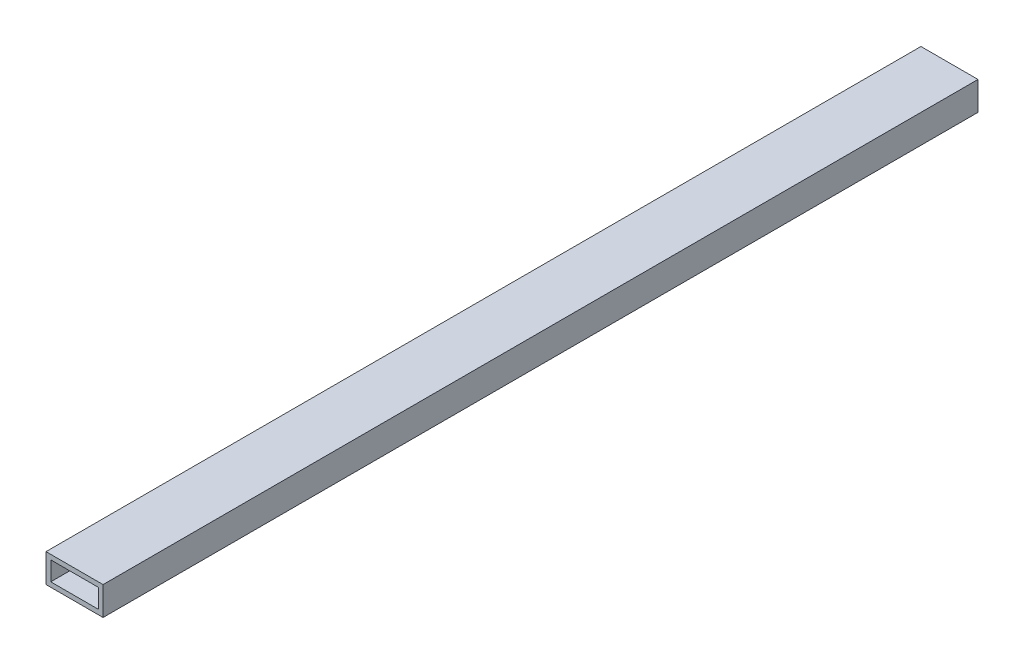
SolidWorks part; units mm, degrees
ref_plane "Front Plane" through (0, 0, 0) normal (0, 0, 1) x (1, 0, 0)
ref_plane "Top Plane" through (0, 0, 0) normal (0, 1, 0) x (1, 0, 0)
ref_plane "Right Plane" through (0, 0, 0) normal (1, 0, 0) x (0, 0, -1)
sketch "Sketch1" plane through (0, 0, 0) normal (0, 0, 1) x (1, 0, 0)
  line L1 (-12.5589, 10.0894) -> (25.5411, 10.0894)
  line L2 (-12.5589, 10.0894) -> (-12.5589, -8.9606)
  line L3 (-12.5589, -8.9606) -> (25.5411, -8.9606)
  line L4 (25.5411, 10.0894) -> (25.5411, -8.9606)
  dimension "D1" = 38.1
  dimension "D2" = 19.05
extrude "Boss-Extrude1" add sketch "Sketch1" along normal blind 584.2 contours L2 L3 L4 L1
sketch "Sketch2" plane through (0, 0, 0) normal (0, 0, -1) x (-1, 0, 0)
  line L8 (9.3839, 6.9144) -> (-22.3661, 6.9144)
  line L9 (-22.3661, 6.9144) -> (-22.3661, -5.7856)
  line L10 (-22.3661, -5.7856) -> (9.3839, -5.7856)
  line L11 (9.3839, -5.7856) -> (9.3839, 6.9144)
  line L12 (9.3839, 6.9144) -> (-22.3661, 6.9144)
  line L13 (-22.3661, 6.9144) -> (-22.3661, -5.7856)
  line L14 (-22.3661, -5.7856) -> (9.3839, -5.7856)
  line L15 (9.3839, -5.7856) -> (9.3839, 6.9144)
  dimension "D1" = 3.175
extrude "Cut-Extrude1" cut sketch "Sketch2" against normal through all
